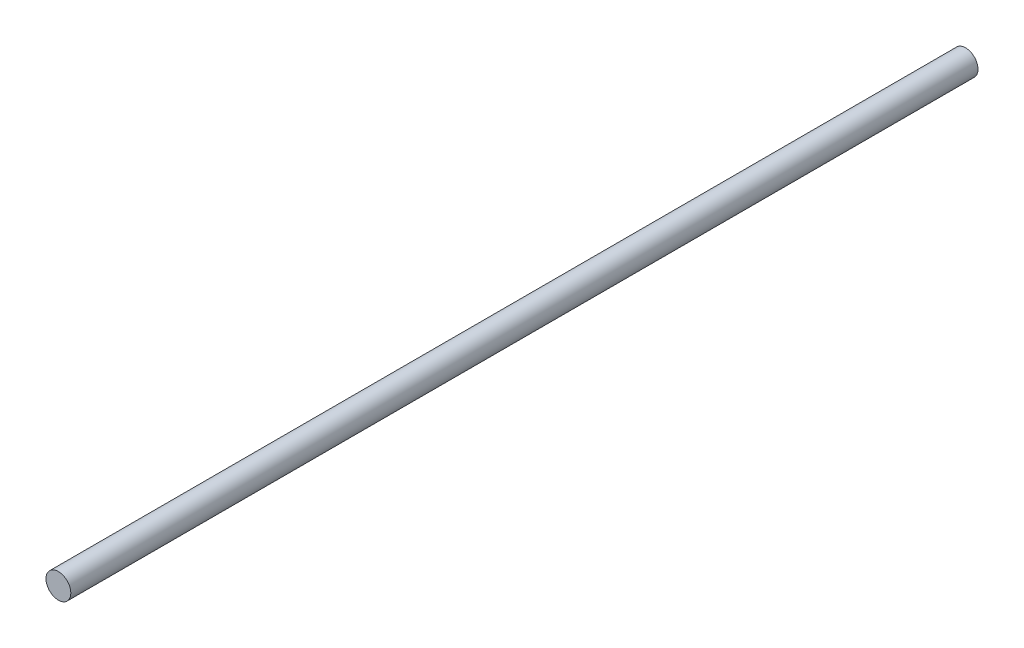
SolidWorks part; units mm, degrees
ref_plane "Front Plane" through (0, 0, 0) normal (0, 0, 1) x (1, 0, 0)
ref_plane "Top Plane" through (0, 0, 0) normal (0, 1, 0) x (1, 0, 0)
ref_plane "Right Plane" through (0, 0, 0) normal (1, 0, 0) x (0, 0, -1)
sketch "Sketch2" plane through (0, 0, 0) normal (0, 0, 1) x (1, 0, 0)
  circle A0 centre (0, 0) radius 0.6604
  dimension "D1" = 1.3208
extrude "Boss-Extrude1" add sketch "Sketch2" along normal blind 48.26
